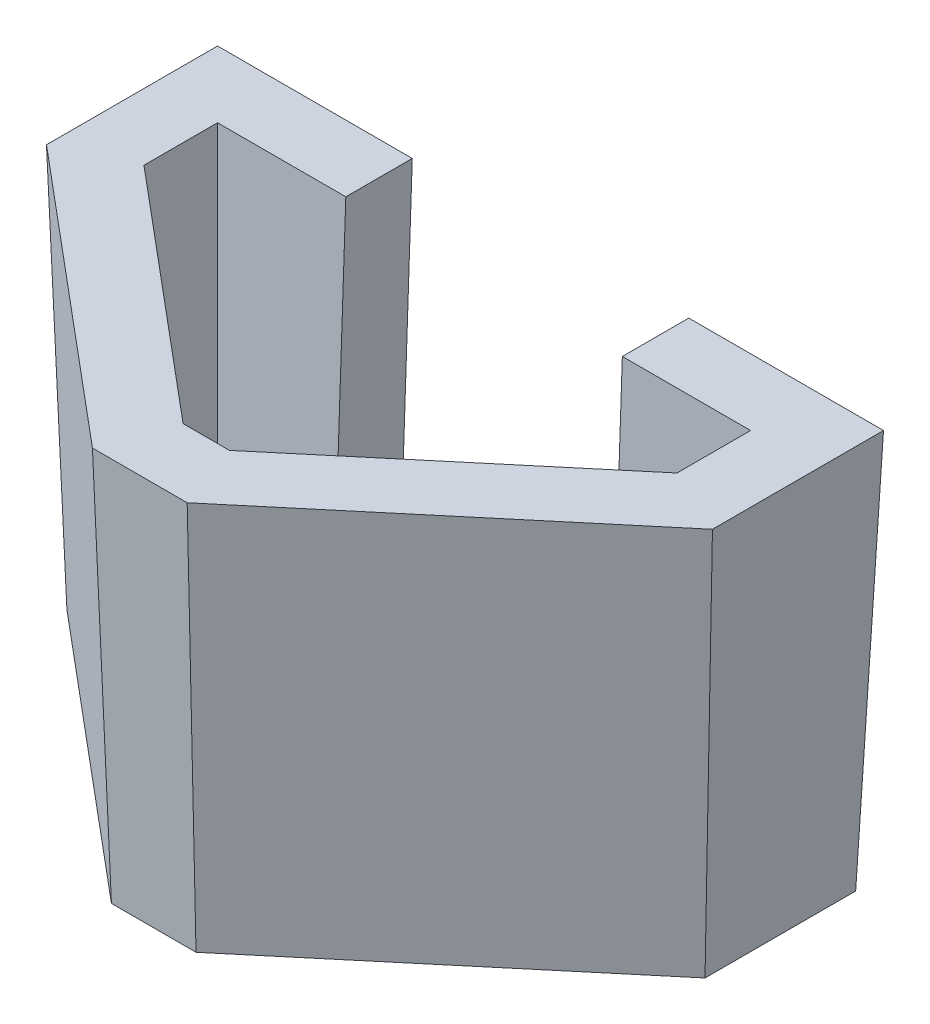
SolidWorks part; units mm, degrees
ref_plane "Alzado" through (0, 0, 0) normal (0, 0, 1) x (1, 0, 0)
ref_plane "Planta" through (0, 0, 0) normal (0, 1, 0) x (1, 0, 0)
ref_plane "Vista lateral" through (0, 0, 0) normal (1, 0, 0) x (0, 0, -1)
sketch "Croquis0" plane through (0, 0, 0) normal (1, 0, 0) x (0, 0, -1)
  line L0 (0, 0) -> (0, 100) construction
  line L1 (0, 0) -> (-3.4921, 100)
  dimension "D1" = 2
  dimension "D2" = 100
  dimension "D3" = 100
sketch "Croquis2" plane through (0, 0, 0) normal (0, 1, 0) x (1, 0, 0)
  line L0 (0, 0) -> (95, 0) construction
  line L1 (95, 0) -> (95, -10) construction
  line L2 (95, -10) -> (50.9051, -47) construction
  line L3 (50.9051, -47) -> (44.0949, -47) construction
  line L4 (44.0949, -47) -> (0, -10) construction
  line L5 (0, -10) -> (0, 0) construction
  line L6 (47.5, 0) -> (47.5, -100.0838) construction
  line L7 (0, -10) -> (14.9783, -10) construction
  line L8 (-12.5, 12.5) -> (107.5, 12.5)
  line L9 (107.5, 12.5) -> (107.5, -15.8288)
  line L10 (107.5, -15.8288) -> (55.4547, -59.5)
  line L11 (55.4547, -59.5) -> (39.5453, -59.5)
  line L12 (39.5453, -59.5) -> (-12.5, -15.8288)
  line L13 (-12.5, -15.8288) -> (-12.5, 12.5)
  dimension "D1" = 95
  dimension "D2" = 10
  dimension "D3" = 47
  dimension "D4" = 40
  dimension "D5" = 12.5
extrude "Saliente-Extruir1" add sketch "Croquis2" along normal blind 75 draft 2 draft outward yes
sketch "Croquis3" plane through (0, 75, 0) normal (0, 1, 0) x (1, 0, 0)
  line L12 (-2.6191, 2.6191) -> (-2.6191, -11.2213)
  line L13 (-2.6191, -11.2213) -> (43.1416, -49.6191)
  line L14 (43.1416, -49.6191) -> (51.8584, -49.6191)
  line L15 (51.8584, -49.6191) -> (97.6191, -11.2213)
  line L16 (97.6191, -11.2213) -> (97.6191, 2.6191)
  line L17 (97.6191, 2.6191) -> (-2.6191, 2.6191)
  line L18 (-2.6191, 2.6191) -> (-2.6191, -11.2213)
  line L19 (-2.6191, -11.2213) -> (43.1416, -49.6191)
  line L20 (43.1416, -49.6191) -> (51.8584, -49.6191)
  line L21 (51.8584, -49.6191) -> (97.6191, -11.2213)
  line L22 (97.6191, -11.2213) -> (97.6191, 2.6191)
  line L23 (97.6191, 2.6191) -> (-2.6191, 2.6191)
  dimension "D1" = 12.5
extrude "Cortar-Extruir1" cut sketch "Croquis3" against normal through all draft 2
sketch "Croquis4" plane through (0, 75, 0) normal (0, 1, 0) x (1, 0, 0)
  line L6 (-15.1191, 15.1191) -> (-15.1191, -17.0501)
  line L7 (-15.1191, -17.0501) -> (38.592, -62.1191)
  line L8 (38.592, -62.1191) -> (56.408, -62.1191)
  line L9 (56.408, -62.1191) -> (110.1191, -17.0501)
  line L10 (110.1191, -17.0501) -> (110.1191, 15.1191)
  line L11 (110.1191, 15.1191) -> (-15.1191, 15.1191)
  line L12 (-15.1191, 15.1191) -> (-15.1191, -17.0501)
  line L13 (-15.1191, -17.0501) -> (38.592, -62.1191)
  line L14 (38.592, -62.1191) -> (56.408, -62.1191)
  line L15 (56.408, -62.1191) -> (110.1191, -17.0501)
  line L16 (110.1191, -17.0501) -> (110.1191, 15.1191)
  line L17 (110.1191, 15.1191) -> (-15.1191, 15.1191)
  dimension "D1" = 0
sketch "Croquis8" plane through (0, 0, 0) normal (1, 0, 0) x (0, 0, -1)
  line L0 (0, 0) -> (3.0936, 88.5898)
  line L1 (0, 0) -> (0, 84.0493) construction
  dimension "D1" = 2
sketch "Croquis5" plane through (0, 0, 0) normal (0, -1, 0) x (1, 0, 0)
  line L0 (95, 0) -> (0, 0) construction
  line L2 (21.5, 0) -> (21.5, -12.5)
  line L3 (107.5, -12.5) -> (-12.5, -12.5) construction
  line L5 (21.5, -12.5) -> (73.5, -12.5)
  line L18 (73.5, -12.5) -> (73.5, 0)
  line L19 (73.5, 0) -> (21.5, 0)
  line L20 (-12.5, -12.5) -> (21.5, -12.5) construction
  line L21 (73.5, -12.5) -> (107.5, -12.5) construction
  dimension "D1" = 52
extrude "Cortar-Extruir2" cut sketch "Croquis5" along direction (0, 0.9994, -0.0349) on the side against the normal through all
sketch "Croquis6" plane through (0, 75, 0) normal (0, 1, 0) x (1, 0, 0)
  line L0 (-15.1191, 15.1191) -> (-2.6191, 2.6191)
  line L1 (97.6191, 2.6191) -> (110.1191, 15.1191)
  line L2 (-2.6191, -11.2213) -> (-2.6191, -27.5389)
  line L3 (97.6191, -11.2213) -> (97.6191, -27.5389)
  line L4 (23.6951, -49.6191) -> (71.3049, -49.6191)
  line L5 (43.1416, -49.6191) -> (51.8584, -49.6191) construction
  line L6 (0, 0) -> (-2.6191, 0)
  line L7 (-15.1191, -17.0501) -> (38.592, -62.1191) construction
  line L8 (56.408, -62.1191) -> (110.1191, -17.0501) construction
  line L9 (21.5, 2.6191) -> (21.5, 15.1191) construction
  line L10 (73.5, 15.1191) -> (73.5, 2.6191) construction
  line L11 (73.5, 15.1191) -> (73.5, 2.6191)
  line L12 (21.5, 2.6191) -> (21.5, 15.1191)
  line L13 (-2.6191, 2.6191) -> (-2.6191, -11.2213) construction
  line L14 (-2.6191, -27.5389) -> (-15.1191, -17.0501)
  line L15 (-15.1191, -17.0501) -> (-15.1191, 15.1191)
  line L16 (97.6191, -27.5389) -> (110.1191, -17.0501)
  line L17 (110.1191, -17.0501) -> (110.1191, 15.1191)
  line L18 (-2.6191, 0) -> (-2.6191, 2.6191)
  line L19 (-2.6191, -11.2213) -> (43.1416, -49.6191) construction
  line L20 (-15.1191, -17.0501) -> (38.592, -62.1191) construction
  line L21 (-2.6191, -27.5389) -> (23.6951, -49.6191)
  line L22 (-2.6191, -11.2213) -> (43.1416, -49.6191)
  line L23 (38.592, -62.1191) -> (23.6951, -49.6191)
  line L24 (56.408, -62.1191) -> (110.1191, -17.0501) construction
  line L25 (38.592, -62.1191) -> (56.408, -62.1191) construction
  line L26 (56.408, -62.1191) -> (71.3049, -49.6191)
  line L27 (38.592, -62.1191) -> (56.408, -62.1191)
  line L28 (97.6191, -27.5389) -> (110.1191, -17.0501)
  dimension "D1" = 36.6191
  dimension "D2" = 52
  dimension "D3" = 36.6191
  dimension "D4" = 24.1191
  dimension "D5" = 24.1191
  dimension "D6" = 16.3176
  dimension "D7" = 32.1692
  dimension "D8" = 17.6777
  dimension "D9" = 30.1579
  dimension "D10" = 32.1692
  dimension "D11" = 17.6777
  dimension "D12" = 30.1579
  dimension "D13" = 16.3176
  dimension "D14" = 34.3507
  dimension "D15" = 59.7363
  dimension "D16" = 19.4465
  dimension "D17" = 16.3176
  dimension "D18" = 12.5
  dimension "D19" = 19.4465
  dimension "D20" = 47.6098
  dimension "D21" = 17.816
sketch "Croquis7" plane through (0, 0, 0) normal (0, -1, 0) x (1, 0, 0)
  line L0 (-12.5, -12.5) -> (0, 0)
  line L1 (0, 10) -> (0, 26.3176)
  line L2 (-12.5, 15.8288) -> (39.5453, 59.5) construction
  line L3 (107.5, -12.5) -> (95, 0)
  line L4 (95, 10) -> (95, 26.3176)
  line L5 (55.4547, 59.5) -> (107.5, 15.8288) construction
  line L6 (24.6483, 47) -> (70.3517, 47)
  line L7 (44.0949, 47) -> (50.9051, 47) construction
  line L8 (0, 26.3176) -> (24.6483, 47)
  line L9 (0, 10) -> (44.0949, 47)
  line L10 (95, 10) -> (50.9051, 47)
  line L11 (50.9051, 47) -> (95, 10) construction
  line L12 (73.5, 0) -> (73.5, -12.5) construction
  line L13 (21.5, -12.5) -> (21.5, 0) construction
  line L14 (73.5, 0) -> (73.5, -12.5)
  line L15 (21.5, -12.5) -> (21.5, 0)
  line L16 (-12.5, -12.5) -> (-12.5, 15.8288)
  line L17 (-12.5, 15.8288) -> (0, 26.3176)
  line L18 (107.5, -12.5) -> (107.5, 15.8288)
  line L19 (107.5, 15.8288) -> (95, 26.3176)
  line L20 (39.5453, 59.5) -> (55.4547, 59.5) construction
  line L21 (39.5453, 59.5) -> (55.4547, 59.5)
  point P34 (63.4655, 47)
  dimension "D1" = 34
  dimension "D2" = 17.6777
  dimension "D3" = 52
  dimension "D4" = 34
  dimension "D5" = 21.5
  dimension "D6" = 21.5
  dimension "D7" = 28.3288
  dimension "D8" = 16.3176
  dimension "D9" = 26.3176
  dimension "D10" = 28.3288
  dimension "D11" = 16.3176
  dimension "D12" = 26.3176
  dimension "D13" = 57.5618
  dimension "D14" = 32.1761
  dimension "D15" = 19.4465
  dimension "D16" = 16.3176
  dimension "D17" = 16.3176
  dimension "D18" = 57.5618
  dimension "D19" = 19.4465
  dimension "D20" = 32.1761
  dimension "D21" = 45.7033
  dimension "D22" = 15.9095
  dimension "D23" = 19.4465
  dimension "D24" = 12.5
sketch "Croquis9" plane through (0, -0.436, -12.4848) normal (0, -0.0349, -0.9994) x (-1, 0, 0)
  line L0 (12.5, 97.9252) -> (12.5, 0.4362)
  line L1 (-73.5, 75.482) -> (-110.1191, 75.482)
  line L4 (-107.5, 0.4362) -> (-73.5, 0.4362)
  line L5 (-73.5, 0.4362) -> (-73.5, 75.482)
  line L6 (-73.5, 75.482) -> (-110.1191, 75.482)
  line L7 (-110.1191, 75.482) -> (-107.5, 0.4362)
  line L8 (-107.5, 0.4362) -> (-73.5, 0.4362)
  line L9 (-73.5, 0.4362) -> (-73.5, 75.482)
  line L10 (-73.5, 75.482) -> (-110.1191, 75.482)
  line L11 (-110.1191, 75.482) -> (-107.5, 0.4362)
  line L12 (15.1191, 75.482) -> (-21.5, 75.482)
  line L13 (-21.5, 75.482) -> (-21.5, 0.4362)
  line L14 (-21.5, 0.4362) -> (12.5, 0.4362)
  line L15 (12.5, 0.4362) -> (15.1191, 75.482)
  line L16 (15.1191, 75.482) -> (-21.5, 75.482)
  line L17 (-21.5, 75.482) -> (-21.5, 0.4362)
  line L18 (-21.5, 0.4362) -> (12.5, 0.4362)
  line L19 (12.5, 0.4362) -> (15.1191, 75.482)
  dimension "D3" = 34
  dimension "D4" = 34
  dimension "D5" = 36.6191
  dimension "D1" = 0
  dimension "D2" = 0
sketch "Croquis11" plane through (107.3691, -3.7494, 0) normal (0.9994, -0.0349, 0) x (0, 0, -1)
  line L5 (-15.8288, 3.7517) -> (12.5, 3.7517)
  line L6 (12.5, 3.7517) -> (15.1191, 78.7974)
  line L7 (15.1191, 78.7974) -> (-17.0501, 78.7974)
  line L8 (-17.0501, 78.7974) -> (-15.8288, 3.7517)
  line L9 (-15.8288, 3.7517) -> (12.5, 3.7517)
  line L10 (12.5, 3.7517) -> (15.1191, 78.7974)
  line L11 (15.1191, 78.7974) -> (-17.0501, 78.7974)
  line L12 (-17.0501, 78.7974) -> (-15.8288, 3.7517)
  dimension "D1" = 0
sketch "Croquis12" plane through (0, 0, 0) normal (0, 1, 0) x (1, 0, 0)
  line L0 (95, 0) -> (97.6191, 0)
  line L1 (97.6191, -11.2213) -> (97.6191, 2.6191) construction
  line L2 (97.6191, 0) -> (97.6191, 2.6191)
  dimension "D1" = 2.6191
  dimension "D2" = 2.6191
sketch "Croquis13" plane through (0, 75, 0) normal (0, 1, 0) x (1, 0, 0)
  line L0 (-15.1191, -17.0501) -> (-12.5, -17.0501)
  line L1 (-12.5, -17.0501) -> (-12.5, -15.8288)
  line L5 (70.3517, -47) -> (70.3517, -49.6191)
  line L6 (23.6951, -49.6191) -> (71.3049, -49.6191) construction
  line L7 (70.3517, -49.6191) -> (71.3049, -49.6191)
  line L8 (38.592, -62.1191) -> (38.592, -59.5)
  line L9 (38.592, -59.5) -> (39.5453, -59.5)
  dimension "D1" = 2.6191
  dimension "D2" = 1.2213
  dimension "D3" = 0.9533
  dimension "D4" = 2.6191
  dimension "D5" = 2.6191
  dimension "D6" = 0.9533
